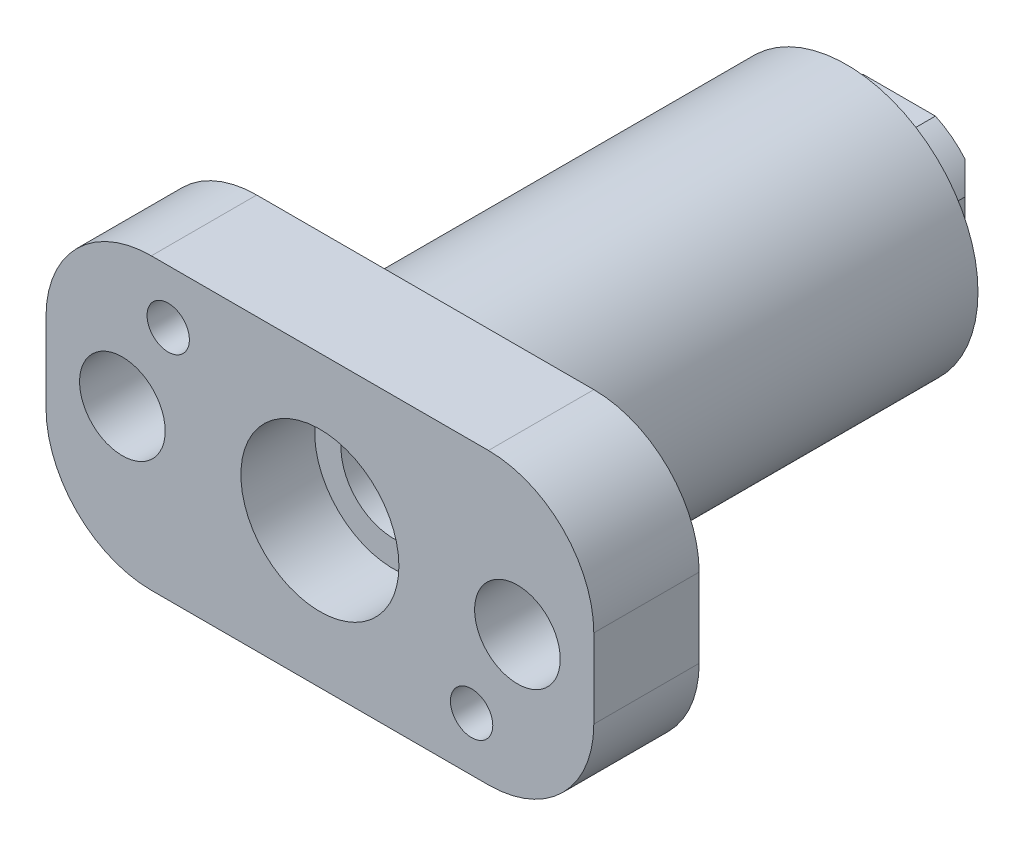
SolidWorks part; units mm, degrees
material "17-4 PH SSTL, H 1150"
ref_plane "XY" through (0, 0, 0) normal (0, 0, 1) x (1, 0, 0)
ref_plane "XZ" through (0, 0, 0) normal (0, 1, 0) x (1, 0, 0)
ref_plane "YZ" through (0, 0, 0) normal (1, 0, 0) x (0, 0, -1)
sketch "Sketch1" plane through (0, 0, 0) normal (0, 0, 1) x (1, 0, 0)
  circle A0 centre (0, 0) radius 15.8369
  dimension "D1" = 31.6738
extrude "Extrude1" add sketch "Sketch1" along normal blind 25.4
sketch "Sketch2" plane through (0, 0, 25.4) normal (0, 0, 1) x (1, 0, 0)
  line L0 (0, 0) -> (0, 33.9226) construction
  line L1 (-33.02, 17.4625) -> (33.02, 17.4625)
  line L2 (33.02, -17.4625) -> (-33.02, -17.4625)
  line L3 (-33.02, 17.4625) -> (-33.02, -17.4625)
  line L4 (33.02, 17.4625) -> (33.02, -17.4625)
  line L5 (0, 0) -> (40.8325, 0) construction
  dimension "D3" = 34.925
  dimension "D4" = 66.04
extrude "Extrude2" add sketch "Sketch2" along normal blind 12.7
sketch "Sketch3" plane through (0, 0, 0) normal (0, 1, 0) x (1, 0, 0)
  line L0 (0, 0) -> (0, 38.5132) construction
  line L1 (0, 0) -> (0, 31.75)
  line L2 (9.4615, 25.4) -> (15.8369, 25.4)
  line L3 (15.8369, 25.4) -> (15.8369, 0)
  line L4 (15.8369, 0) -> (0, 0)
  line L6 (15.8369, 0) -> (-15.8369, 0) construction
  line L7 (9.4615, 25.4) -> (9.4615, 31.75)
  line L8 (9.4615, 31.75) -> (0, 31.75)
  dimension "D1" = 25.4
  dimension "D2" = 31.6738
  dimension "D3" = 31.6738
  dimension "D4" = 18.923
  dimension "D5" = 6.35
revolve "Revolve1" add sketch "Sketch3" angle 360 about L0
sketch "Sketch4" plane through (0, 0, 38.1) normal (0, 0, 1) x (1, 0, 0)
  circle A0 centre (0, 0) radius 6.35
  dimension "D1" = 12.7
extrude "Cut-Extrude1" cut sketch "Sketch4" against normal through all
sketch "Sketch6" plane through (0, 0, 38.1) normal (0, 0, 1) x (1, 0, 0)
  circle A0 centre (0, 0) radius 9.525
  dimension "D1" = 19.05
extrude "Cut-Extrude5" cut sketch "Sketch6" against normal blind 8.89
sketch "Sketch7" plane through (0, 0, -25.4) normal (0, 0, -1) x (-1, 0, 0)
  line L0 (-9.4615, 9.4615) -> (9.4615, -9.4615) construction
  line L1 (-9.4615, 9.4615) -> (9.4615, 9.4615)
  line L2 (-9.4615, 9.4615) -> (-9.4615, -9.4615)
  line L3 (-9.4615, -9.4615) -> (9.4615, -9.4615)
  line L4 (9.4615, 9.4615) -> (9.4615, -9.4615)
  circle A0 centre (0, 0) radius 9.4615 construction
  circle A1 centre (0, 0) radius 6.35 construction
  circle A2 centre (0, 0) radius 6.35
extrude "Extrude3" add sketch "Sketch7" along normal up to surface (6.35 mm away) up to face at (6.35, 0, -31.75)
sketch "Sketch9" plane through (0, 0, -31.75) normal (0, 0, -1) x (-1, 0, 0)
  circle A0 centre (0, 0) radius 10.414
  dimension "D1" = 20.828
extrude "Cut-Extrude7" cut sketch "Sketch9" against normal up to surface (6.35 mm away) flip side to cut up to face at (15.8369, 0, -25.4)
fillet "Fillet1" radius 12.7 4 edges at (33.02, -17.4625, 31.75) (33.02, 17.4625, 31.75) (-33.02, 17.4625, 31.75) (-33.02, -17.4625, 31.75)
hole_wizard "1/4-20 Tapped Hole1" positions "Sketch12" profile "Sketch11" tap size "1/4-20" standard "Ansi Inch" end condition through all
sketch "Sketch12" plane through (0, 0, 38.1) normal (0, 0, 1) x (1, 0, 0)
  line L0 (-18.288, 10.9855) -> (-18.288, -10.9855) construction
  line L1 (-18.288, -10.9855) -> (18.288, -10.9855) construction
  line L2 (0, 0) -> (-18.288, 0) construction
  line L3 (0, 0) -> (0, -10.9855) construction
  point P0 (18.288, -10.9855)
  point P1 (-18.288, 10.9855)
  dimension "D1" = 21.971
  dimension "D2" = 36.576
sketch "Sketch11" plane through (18.288, -10.9855, 38.1) normal (1, 0, 0) x (0, -1, 0)
  line L0 (0, 0) -> (0, 69.85)
  line L1 (0, 69.85) -> (2.5527, 69.85)
  line L2 (2.5527, 69.85) -> (2.5527, 0)
  line L5 (2.5527, 0) -> (0, 0)
  line L11 (0, -6.35) -> (0, 107.95) construction
  dimension "Thru Tap Drill Dia." = 5.1054
  dimension "Thru Tap Drill Depth" = 69.85
cosmetic thread "Hole Thread1" parameters "D2"=6.35
cosmetic thread "Hole Thread2" parameters "D2"=6.35
hole_wizard "13/32 (0.40625) Diameter Hole1" positions "Sketch14" profile "Sketch13" hole size "13/32" standard "Ansi Inch" end condition through all
sketch "Sketch14" plane through (0, 0, 38.1) normal (0, 0, 1) x (1, 0, 0)
  line L0 (-23.8125, 0) -> (0, 0) construction
  line L1 (0, 0) -> (23.8125, 0) construction
  point P0 (-23.8125, 0)
  point P1 (23.8125, 0)
  dimension "D1" = 47.625
sketch "Sketch13" plane through (-23.8125, 0, 38.1) normal (1, 0, 0) x (0, -1, 0)
  line L0 (0, 0) -> (0, 69.85)
  line L1 (0, 69.85) -> (5.1594, 69.85)
  line L2 (5.1594, 69.85) -> (5.1594, 0)
  line L5 (5.1594, 0) -> (0, 0)
  line L11 (0, -6.35) -> (0, 107.95) construction
  dimension "Thru Hole Dia." = 10.3187
  dimension "Thru Hole Depth" = 69.85
chamfer "Chamfer2" distance 1.524 angle 45 2 edges at (-9.4615, 0, -31.75) (9.4615, 0, -31.75)
